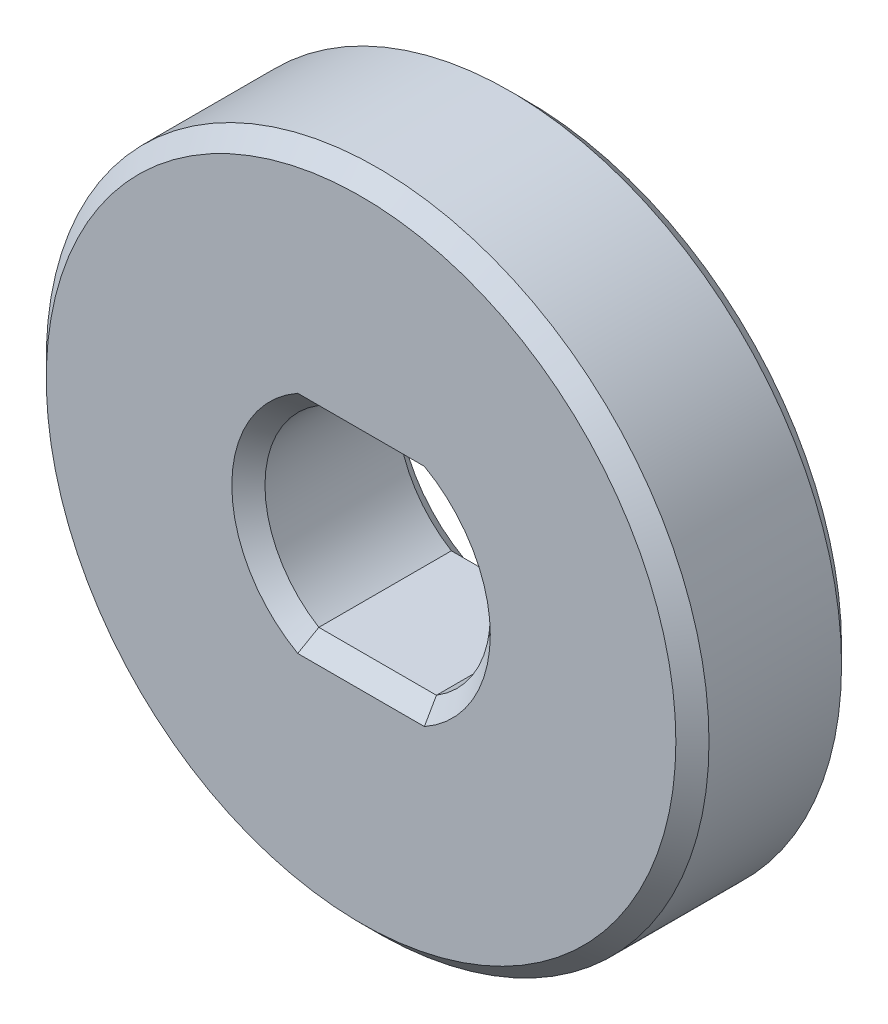
SolidWorks part; units mm, degrees
material "Polylactic Acid (PLA)"
ref_plane "Front Plane" through (0, 0, 0) normal (0, 0, 1) x (1, 0, 0)
ref_plane "Top Plane" through (0, 0, 0) normal (0, 1, 0) x (1, 0, 0)
ref_plane "Right Plane" through (0, 0, 0) normal (1, 0, 0) x (0, 0, -1)
sketch "Sketch1" plane through (0, 0, 0) normal (0, 0, 1) x (1, 0, 0)
  line L0 (-1.7748, 2.9) -> (1.7748, 2.9)
  line L1 (-1.6583, -2.5) -> (1.6583, -2.5) construction
  line L2 (-1.6583, -2.5) -> (-1.6583, 2.5) construction
  line L3 (-1.6583, 2.5) -> (1.6583, 2.5) construction
  line L4 (1.6583, -2.5) -> (1.6583, 2.5) construction
  line L5 (-1.6583, -2.5) -> (1.6583, 2.5) construction
  line L6 (-1.6583, 2.5) -> (1.6583, -2.5) construction
  line L7 (-1.7748, -2.9) -> (1.7748, -2.9)
  circle A0 centre (0, 0) radius 10
  arc A1 (-1.6583, 2.5) -> (-1.6583, -2.5) centre (0, 0) ccw construction
  arc A2 (1.6583, -2.5) -> (1.6583, 2.5) centre (0, 0) ccw construction
  arc A3 (1.7748, -2.9) -> (1.7748, 2.9) centre (0, 0) ccw
  arc A4 (-1.7748, 2.9) -> (-1.7748, -2.9) centre (0, 0) ccw
  dimension "D1" = 20
  dimension "D2" = 6
  dimension "D3" = 2.5
  dimension "D4" = 0.4
extrude "Boss-Extrude1" add sketch "Sketch1" along normal blind 5
chamfer "Chamfer1" distance 0.5 angle 45 10 edges at (3.4, 0, 0) (0, 2.9, 0) (0, -2.9, 0) (-3.4, 0, 0) (0, 2.9, 5) (-3.4, 0, 5) (3.4, 0, 5) (0, -2.9, 5) (10, 0, 0) (10, 0, 5)
